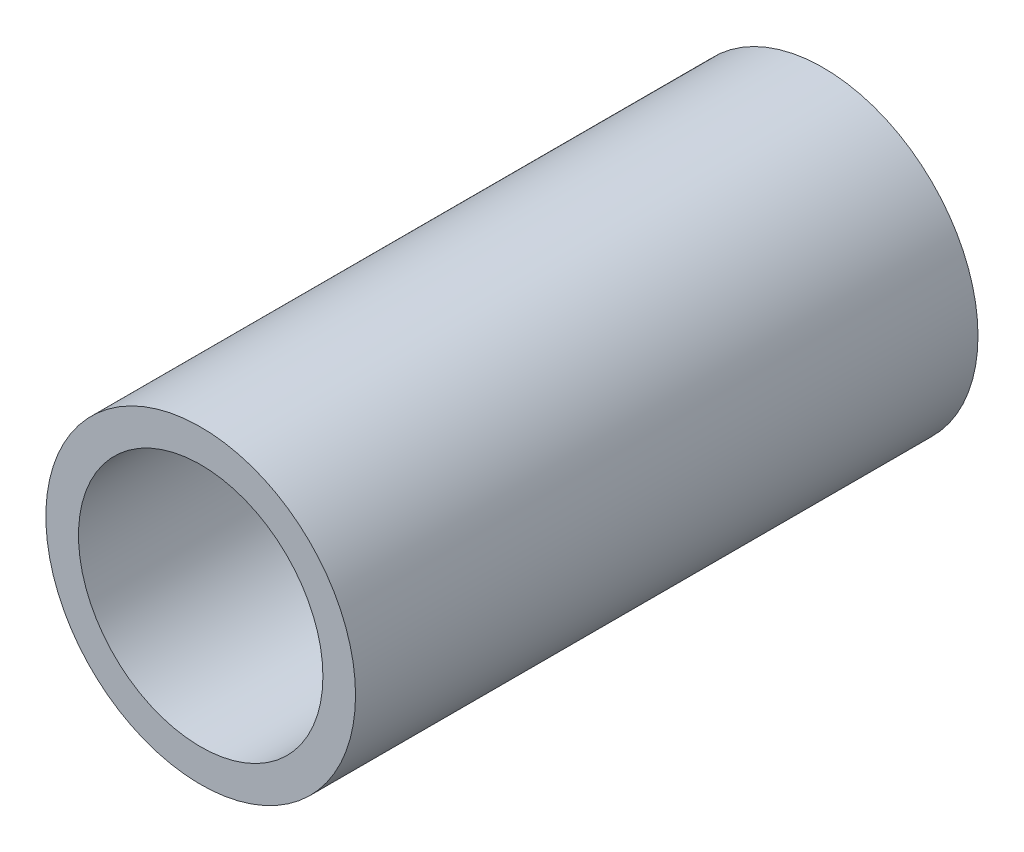
SolidWorks part; units mm, degrees
material "Plain Carbon Steel"
ref_plane "Front Plane" through (0, 0, 0) normal (1, 0, 0) x (0, 1, 0)
ref_plane "Top Plane" through (0, 0, 0) normal (0, 0, 1) x (0, 1, 0)
ref_plane "Right Plane" through (0, 0, 0) normal (0, 1, 0) x (-1, 0, 0)
sketch "Sketch1" plane through (0, 0, 0) normal (0, 0, 1) x (0, 1, 0)
  circle A0 centre (0, 0) radius 10.025
  circle A1 centre (0, 0) radius 12.7
  dimension "D1" = 20.05
  dimension "D2" = 25.4
extrude "Boss-Extrude1" add sketch "Sketch1" along normal blind 50.8 and the other way blind 0.254
